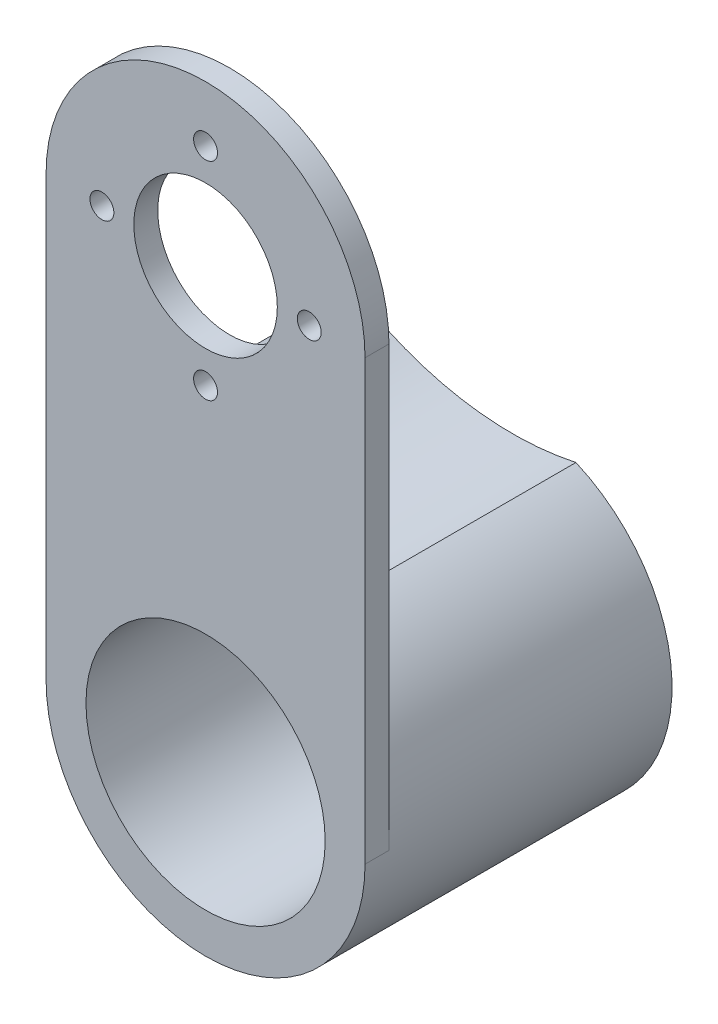
SolidWorks part; units mm, degrees
ref_plane "Face" through (0, 0, 0) normal (0, 0, 1) x (1, 0, 0)
ref_plane "Dessus" through (0, 0, 0) normal (0, 1, 0) x (1, 0, 0)
ref_plane "Droite" through (0, 0, 0) normal (1, 0, 0) x (0, 0, -1)
sketch "Esquisse1" plane through (0, 0, 0) normal (0, 0, 1) x (1, 0, 0)
  line L0 (0, 0) -> (0, 55)
  line L1 (40, 55) -> (40, 0)
  line L2 (20, 75) -> (20, -20) construction
  line L3 (0, 55) -> (40, 55) construction
  line L4 (0, 0) -> (40, 0) construction
  line L5 (20, -20) -> (40, -20) construction
  line L6 (40, -20) -> (20, 0) construction
  line L7 (20, 0) -> (0, 20) construction
  line L8 (40, 0) -> (40, -20) construction
  line L9 (20, -20) -> (0, -20) construction
  line L10 (0, -20) -> (0, 0) construction
  line L11 (0, -20) -> (20, 0) construction
  line L12 (20, 0) -> (40, 20) construction
  arc A0 (0, 55) -> (40, 55) centre (20, 55) cw
  arc A1 (0, 0) -> (40, 0) centre (20, 0) ccw
  circle A2 centre (20, 55) radius 9
  circle A3 centre (20, 0) radius 15
  circle A4 centre (20, 68) radius 1.5
  circle A5 centre (20, 42) radius 1.5
  circle A6 centre (7, 55) radius 1.5
  circle A7 centre (33, 55) radius 1.5
  dimension "D1" = 20
  dimension "D3" = 18
  dimension "D5" = 3
  dimension "D2" = 55
  dimension "D4" = 26
  dimension "D6" = 26
extrude "Extrusion1" add sketch "Esquisse1" along normal blind 3
sketch "Esquisse2" plane through (0, 0, 3) normal (0, 0, 1) x (1, 0, 0)
  line L0 (0, 0) -> (0, 23.2786)
  arc A0 (0, 0) -> (27.9495, 18.3523) centre (20, 0) ccw
  circle A1 centre (20, 0) radius 9
  arc A2 (0, 23.2786) -> (27.9495, 18.3523) centre (20, 55) ccw
extrude "Extrusion2" add sketch "Esquisse2" against normal blind 38.5
sketch "Esquisse3" plane through (0, 0, 3) normal (0, 0, 1) x (1, 0, 0)
  circle A0 centre (20, 0) radius 15
extrude "Extrusion3" cut sketch "Esquisse3" against normal blind 34.5
